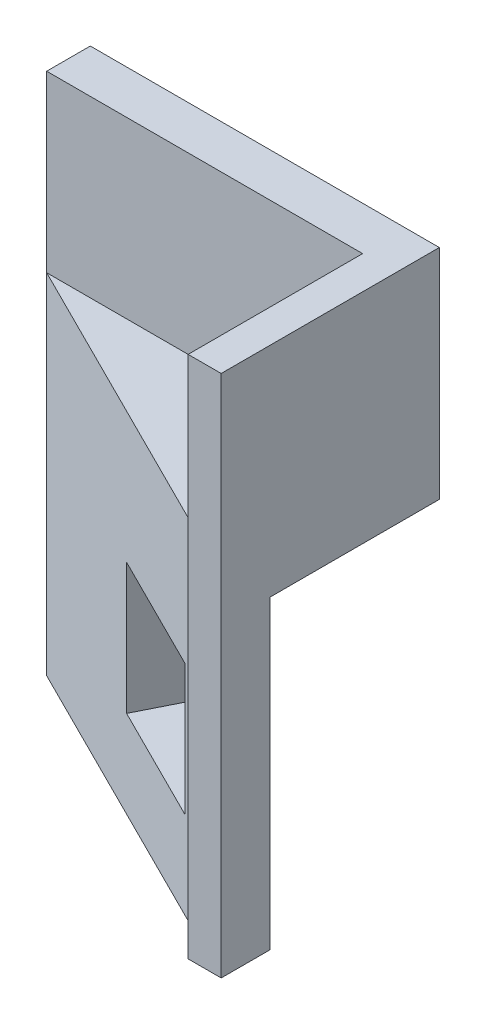
SolidWorks part; units mm, degrees
ref_plane "Front Plane" through (0, 0, 0) normal (0, 0, 1) x (1, 0, 0)
ref_plane "Top Plane" through (0, 0, 0) normal (0, 1, 0) x (1, 0, 0)
ref_plane "Right Plane" through (0, 0, 0) normal (1, 0, 0) x (0, 0, -1)
sketch "Sketch1" plane through (0, 0, 0) normal (0, 0, 1) x (1, 0, 0)
  line L1 (0, 0) -> (50.8, 0)
  line L2 (0, 0) -> (0, -76.2)
  line L3 (0, -76.2) -> (50.8, -76.2)
  line L4 (50.8, 0) -> (50.8, -76.2)
  dimension "D1" = 50.8
  dimension "D2" = 76.2
extrude "Boss-Extrude1" add sketch "Sketch1" along normal blind 6.35
sketch "Sketch2" plane through (0, 0, 6.35) normal (0, 0, 1) x (1, 0, 0)
  line L0 (50.8, -76.2) -> (50.8, 0) construction
  line L1 (0, -76.2) -> (50.8, -76.2)
  line L2 (0, -76.2) -> (0, -25.4)
  line L3 (0, -25.4) -> (50.8, -25.4)
  line L4 (50.8, -76.2) -> (50.8, -25.4)
  dimension "D1" = 50.8
extrude "Boss-Extrude2" add sketch "Sketch2" along normal blind 25.4
sketch "Sketch3" plane through (0, -25.4, 0) normal (0, 1, 0) x (1, 0, 0)
  line L0 (0, -6.35) -> (0, -31.75)
  line L1 (0, -31.75) -> (50.8, -31.75)
  line L2 (50.8, -31.75) -> (0, -6.35)
extrude "Cut-Extrude1" cut sketch "Sketch3" against normal up to next
sketch "Sketch4" plane through (0, 0, 0) normal (0, 0, -1) x (-1, 0, 0)
  line L0 (0, -76.2) -> (-50.8, -76.2) construction
  line L1 (-50.8, 0) -> (-45.9863, 0)
  line L2 (-50.8, 0) -> (-50.8, -76.2)
  line L3 (-50.8, -76.2) -> (-45.9863, -76.2)
  line L4 (-45.9863, 0) -> (-45.9863, -76.2)
extrude "Boss-Extrude3" add sketch "Sketch4" against normal blind 31.75
sketch "Sketch5" plane through (0, -76.2, 0) normal (0, -1, 0) x (1, 0, 0)
  line L0 (50.8, 0) -> (50.8, 24.6505)
  line L1 (50.8, 31.75) -> (50.8, 0) construction
  line L2 (50.8, 24.6505) -> (1.499, 0)
  line L3 (0, 0) -> (50.8, 0) construction
  line L4 (1.499, 0) -> (50.8, 0)
  line L5 (0, 6.35) -> (45.9863, 29.3431) construction
  dimension "D1" = 6.35
extrude "Cut-Extrude2" cut sketch "Sketch5" against normal blind 44.45
sketch "Sketch6" plane through (-2.54, 0, 5.08) normal (-0.4472, 0, 0.8944) x (0.8944, 0, 0.4472)
  line L0 (2.8398, -76.2) -> (54.254, -76.2) construction
  line L1 (28.854, -44.45) -> (47.904, -44.45)
  line L2 (28.854, -44.45) -> (28.854, -63.5)
  line L3 (28.854, -63.5) -> (47.904, -63.5)
  line L4 (47.904, -44.45) -> (47.904, -63.5)
  line L5 (54.254, -76.2) -> (54.254, -25.4) construction
  dimension "D1" = 19.05
  dimension "D2" = 19.05
  dimension "D3" = 12.7
  dimension "D4" = 6.35
extrude "Cut-Extrude3" cut sketch "Sketch6" against normal up to next
